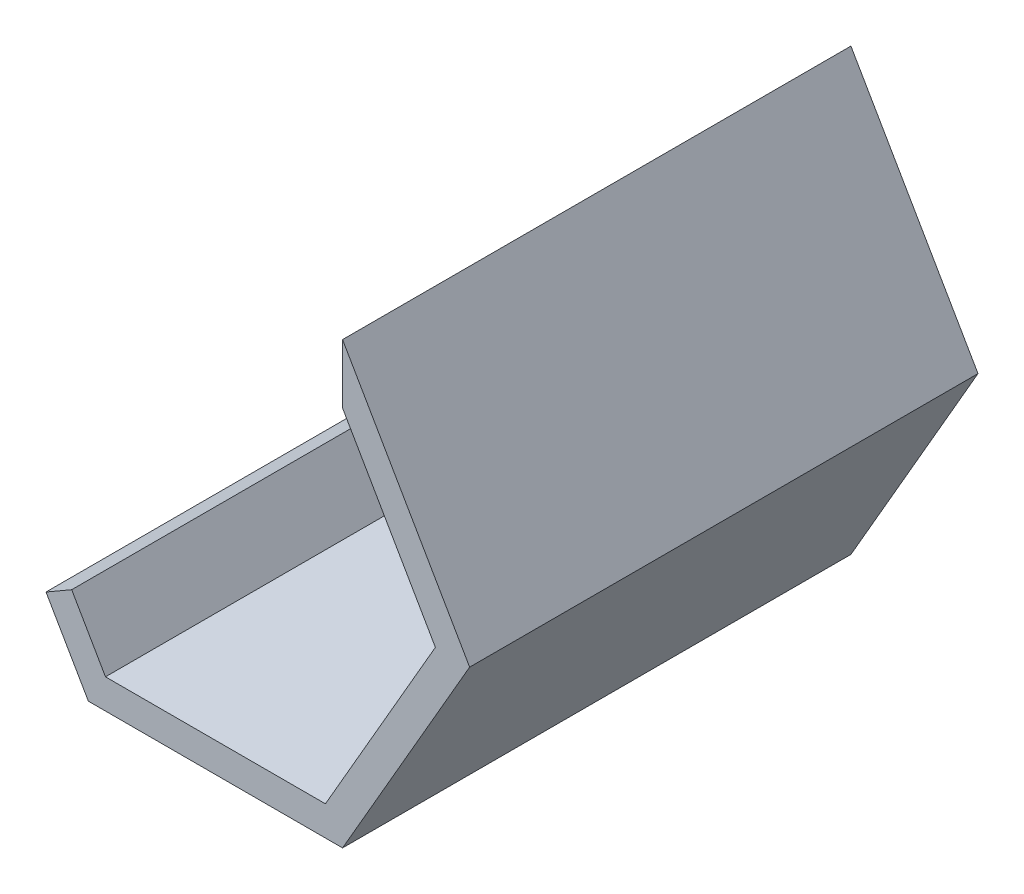
SolidWorks part; units mm, degrees
ref_plane "Alzado" through (0, 0, 0) normal (0, 0, 1) x (1, 0, 0)
ref_plane "Planta" through (0, 0, 0) normal (0, 1, 0) x (1, 0, 0)
ref_plane "Vista lateral" through (0, 0, 0) normal (1, 0, 0) x (0, 0, -1)
sketch "Croquis1" plane through (0, 0, 0) normal (0, 0, 1) x (1, 0, 0)
  line L0 (-148.6168, -25.4664) -> (-88.6168, -25.4664)
  line L1 (-88.6168, -25.4664) -> (-58.6168, 26.4951)
  line L2 (-58.6168, 26.4951) -> (-88.6168, 78.4567)
  line L3 (-148.6168, -25.4664) -> (-158.6168, -8.1459)
  line L4 (-158.6168, -8.1459) -> (-152.5546, -4.6459)
  line L5 (-152.5546, -4.6459) -> (-144.5754, -18.4664)
  line L6 (-144.5754, -18.4664) -> (-92.6583, -18.4664)
  line L7 (-92.6583, -18.4664) -> (-66.6997, 26.4951)
  line L9 (-88.6168, 78.4567) -> (-88.6168, 68.6358)
  line L10 (-82.2801, 53.4811) -> (-88.6168, 64.4567)
  line L11 (-88.6168, 64.4567) -> (-88.6168, 68.6358)
  line L12 (-82.2801, 53.4811) -> (-66.6997, 26.4951)
  dimension "D1" = 120
  dimension "D2" = 120
  dimension "D3" = 120
  dimension "D4" = 7
  dimension "D5" = 7
  dimension "D6" = 7
  dimension "D7" = 20
  dimension "D8" = 60
  dimension "D9" = 60
  dimension "D10" = 60
  dimension "D11" = 30
extrude "Saliente-Extruir1" add sketch "Croquis1" along normal blind 120
